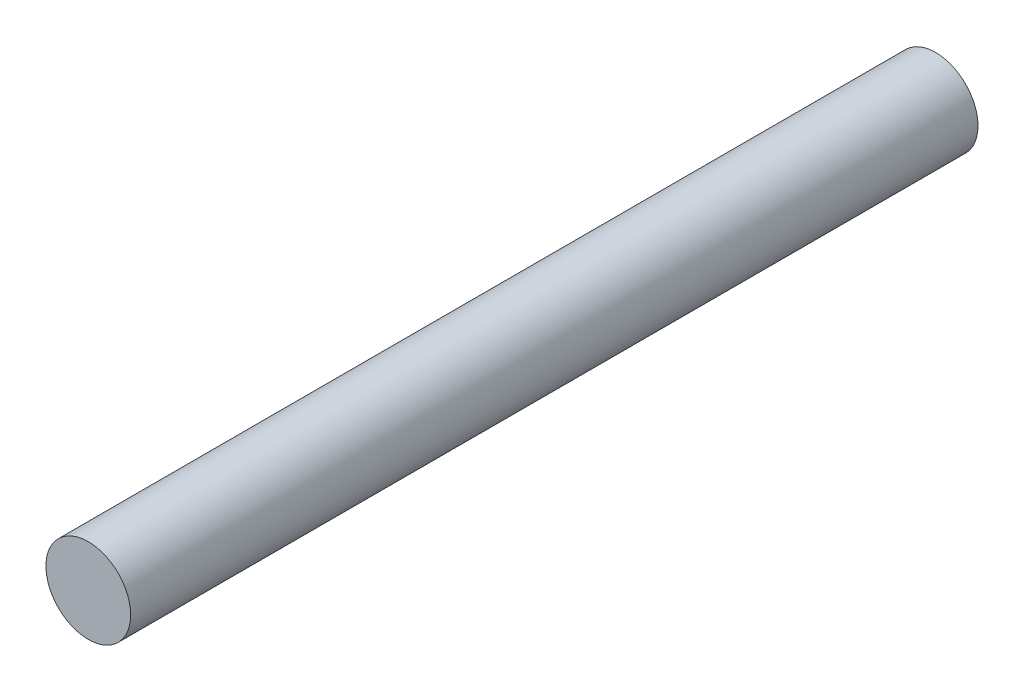
SolidWorks part; units mm, degrees
material "AISI 304"
ref_plane "前视基准面" through (0, 0, 0) normal (0, 0, 1) x (1, 0, 0)
ref_plane "上视基准面" through (0, 0, 0) normal (0, 1, 0) x (1, 0, 0)
ref_plane "右视基准面" through (0, 0, 0) normal (1, 0, 0) x (0, 0, -1)
sketch "草图1" plane through (0, 0, 0) normal (0, 0, 1) x (1, 0, 0)
  circle A0 centre (0, 0) radius 4
  dimension "D1" = 8
extrude "凸台-拉伸1" add sketch "草图1" along normal blind 80
sketch "草图2" plane through (0, 0, 80) normal (0, 0, 1) x (1, 0, 0)
  line L0 (0, 0) -> (0, 13.6972) construction
